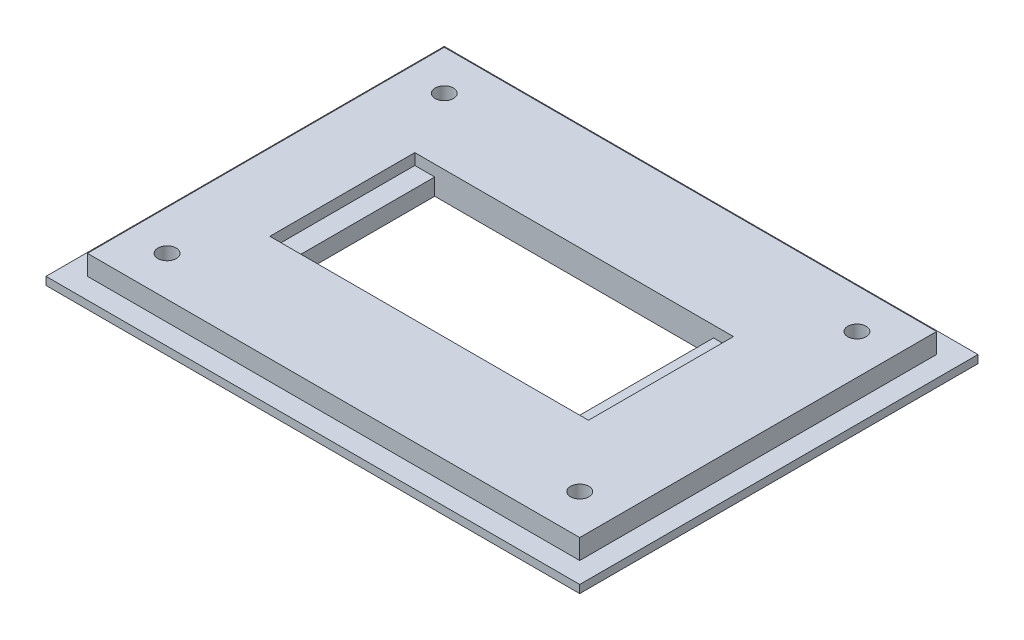
SolidWorks part; units mm, degrees
ref_plane "Front Plane" through (0, 0, 0) normal (0, 0, 1) x (1, 0, 0)
ref_plane "Top Plane" through (0, 0, 0) normal (0, 1, 0) x (1, 0, 0)
ref_plane "Right Plane" through (0, 0, 0) normal (1, 0, 0) x (0, 0, -1)
sketch "Sketch2" plane through (0, 0, 0) normal (0, 1, 0) x (1, 0, 0)
  line L1 (0, 0) -> (85.09, 0)
  line L2 (0, 0) -> (0, 63.5)
  line L3 (0, 63.5) -> (85.09, 63.5)
  line L4 (85.09, 0) -> (85.09, 63.5)
  dimension "D1" = 63.5
  dimension "D2" = 85.09
extrude "Boss-Extrude1" add sketch "Sketch2" along normal blind 1.27
sketch "Sketch3" plane through (0, 1.27, 0) normal (0, 1, 0) x (1, 0, 0)
  line L0 (0, 63.5) -> (0, 0) construction
  line L1 (3.302, 60.198) -> (81.788, 60.198)
  line L2 (3.302, 60.198) -> (3.302, 3.302)
  line L3 (3.302, 3.302) -> (81.788, 3.302)
  line L4 (81.788, 60.198) -> (81.788, 3.302)
  line L5 (85.09, 63.5) -> (0, 63.5) construction
  line L6 (0, 0) -> (85.09, 0) construction
  line L7 (85.09, 0) -> (85.09, 63.5) construction
  dimension "D1" = 3.302
  dimension "D2" = 3.302
  dimension "D3" = 3.302
  dimension "D4" = 3.302
extrude "Boss-Extrude2" add sketch "Sketch3" along normal blind 3.175
sketch "Sketch4" plane through (0, 4.445, 0) normal (0, 1, 0) x (1, 0, 0)
  line L0 (81.788, 60.198) -> (3.302, 60.198) construction
  line L1 (15.494, 43.307) -> (66.294, 43.307)
  line L2 (15.494, 43.307) -> (15.494, 20.193)
  line L3 (15.494, 20.193) -> (66.294, 20.193)
  line L4 (66.294, 43.307) -> (66.294, 20.193)
  line L5 (85.09, 0) -> (85.09, 63.5) construction
  dimension "D1" = 23.114
  dimension "D2" = 50.8
  dimension "D3" = 16.891
  dimension "D4" = 18.796
extrude "Cut-Extrude1" cut sketch "Sketch4" against normal blind 1.778
sketch "Sketch5" plane through (0, 2.667, 0) normal (0, 1, 0) x (1, 0, 0)
  line L0 (66.294, 43.307) -> (15.494, 43.307) construction
  line L1 (18.669, 43.307) -> (63.119, 43.307)
  line L2 (18.669, 43.307) -> (18.669, 20.193)
  line L3 (18.669, 20.193) -> (63.119, 20.193)
  line L4 (63.119, 43.307) -> (63.119, 20.193)
  line L5 (15.494, 20.193) -> (66.294, 20.193) construction
  line L6 (15.494, 43.307) -> (15.494, 20.193) construction
  line L7 (66.294, 20.193) -> (66.294, 43.307) construction
  dimension "D1" = 3.175
  dimension "D2" = 3.175
extrude "Cut-Extrude2" cut sketch "Sketch5" against normal through all
sketch "Sketch6" plane through (0, 4.445, 0) normal (0, 1, 0) x (1, 0, 0)
  line L0 (81.788, 60.198) -> (3.302, 60.198) construction
  line L1 (3.302, 60.198) -> (3.302, 3.302) construction
  line L2 (3.302, 3.302) -> (81.788, 3.302) construction
  line L3 (81.788, 3.302) -> (81.788, 60.198) construction
  line L4 (81.788, 3.302) -> (81.788, 60.198) construction
  circle A0 centre (9.652, 53.848) radius 1.4605
  circle A1 centre (9.652, 9.652) radius 1.4605
  circle A2 centre (75.438, 53.848) radius 1.4605
  circle A3 centre (75.438, 9.652) radius 1.4605
  dimension "D1" = 2.921
  dimension "D4" = 2.921
  dimension "D7" = 2.921
  dimension "D10" = 2.921
  dimension "D2" = 6.35
  dimension "D3" = 6.35
  dimension "D5" = 6.35
  dimension "D6" = 6.35
  dimension "D8" = 6.35
  dimension "D9" = 6.35
  dimension "D11" = 6.35
  dimension "D12" = 6.35
extrude "Cut-Extrude3" cut sketch "Sketch6" against normal through all
